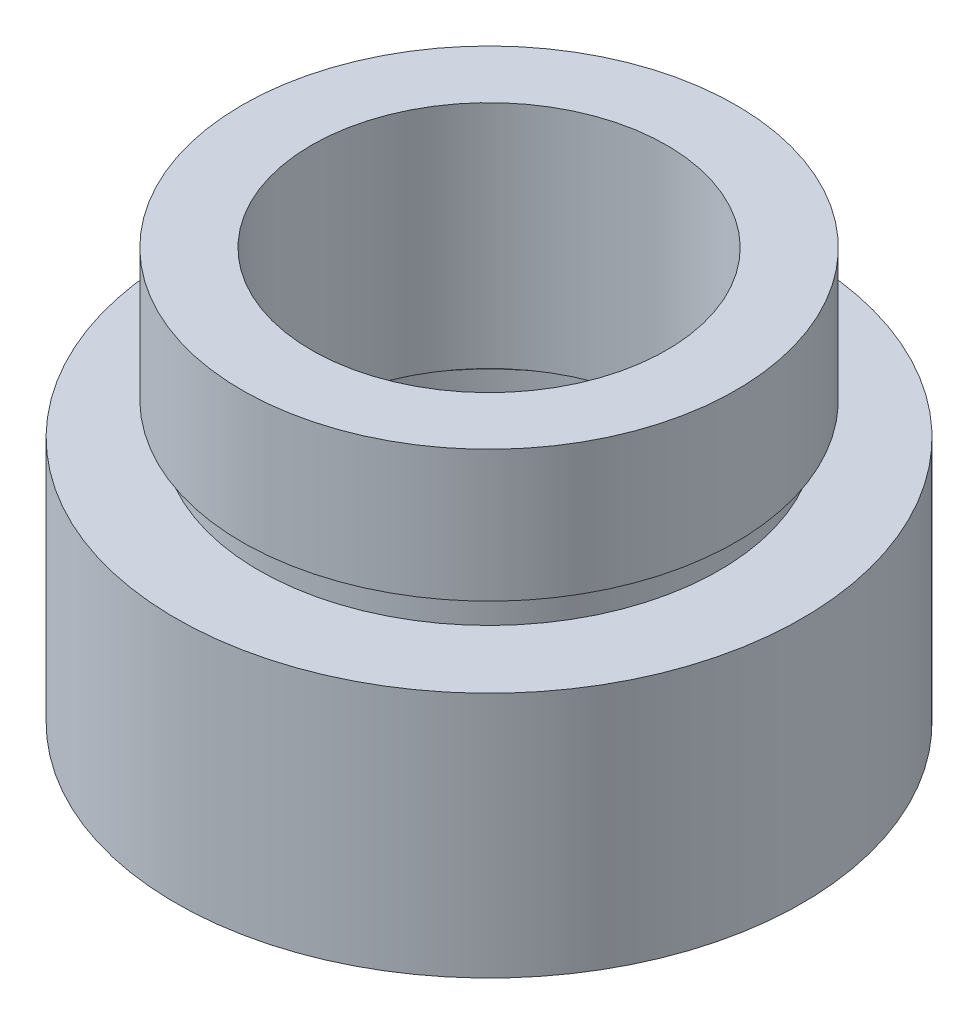
SolidWorks part; units mm, degrees
ref_plane "前视基准面" through (0, 0, 0) normal (0, 0, 1) x (1, 0, 0)
ref_plane "上视基准面" through (0, 0, 0) normal (0, 1, 0) x (1, 0, 0)
ref_plane "右视基准面" through (0, 0, 0) normal (1, 0, 0) x (0, 0, -1)
sketch "草图1" plane through (0, 0, 0) normal (0, 0, 1) x (1, 0, 0)
  line L0 (0, 16.886) -> (0, -24.4878) construction
  line L1 (6.795, 0) -> (6.795, 4.5)
  line L2 (6.9, 4.5) -> (6.9, 5.5)
  line L3 (6.795, 4.5) -> (6.9, 4.5)
  line L4 (5.4, 12.5) -> (5.4, 5.5)
  line L5 (7.51, 12.5) -> (7.51, 8.5)
  line L6 (7.51, 8.5) -> (7, 8.5)
  line L7 (7, 8.5) -> (7, 7.5)
  line L8 (7, 7.5) -> (9.525, 7.5)
  line L9 (9.525, 7.5) -> (9.525, 0)
  line L10 (9.525, 0) -> (6.795, 0)
  line L11 (5.4, 12.5) -> (7.51, 12.5)
  line L12 (5.4, 5.5) -> (6.9, 5.5)
  line L13 (0, 0) -> (3.4668, 0) construction
  point P4 (8.16, 0)
  dimension "D1" = 6.795
  dimension "D2" = 7.51
  dimension "D3" = 7
  dimension "D4" = 6.9
  dimension "D5" = 1
  dimension "D6" = 9.525
  dimension "D7" = 5.4
  dimension "D8" = 7.5
  dimension "D9" = 1
  dimension "D10" = 12.5
  dimension "D11" = 7
revolve "旋转1" add sketch "草图1" angle 360 about L0
cosmetic thread "装饰螺纹线1" parameters "D2"=15
cosmetic thread "装饰螺纹线2" parameters "D2"=11
cosmetic thread "装饰螺纹线3" parameters "D2"=14
